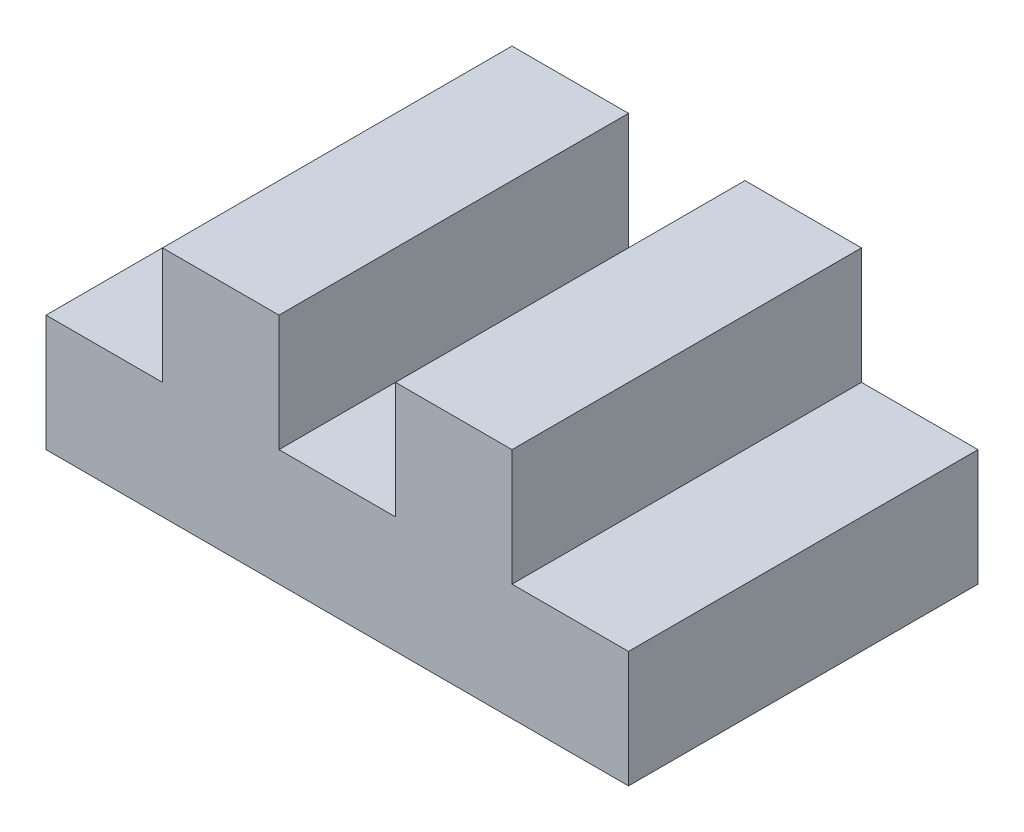
SolidWorks part; units mm, degrees
ref_plane "Front Plane" through (0, 0, 0) normal (0, 0, 1) x (1, 0, 0)
ref_plane "Top Plane" through (0, 0, 0) normal (0, 1, 0) x (1, 0, 0)
ref_plane "Right Plane" through (0, 0, 0) normal (1, 0, 0) x (0, 0, -1)
sketch "Sketch2" plane through (0, 0, 0) normal (0, 0, 1) x (1, 0, 0)
  line L0 (0, 0) -> (50, 0)
  line L1 (50, 0) -> (50, 10)
  line L2 (50, 10) -> (40, 10)
  line L3 (40, 10) -> (40, 20)
  line L4 (40, 20) -> (30, 20)
  line L5 (30, 20) -> (30, 10)
  line L6 (30, 10) -> (20, 10)
  line L7 (20, 10) -> (20, 20)
  line L8 (20, 20) -> (10, 20)
  line L9 (10, 20) -> (10, 10)
  line L10 (10, 10) -> (0, 10)
  line L11 (0, 10) -> (0, 0)
  dimension "D1" = 10
extrude "Boss-Extrude1" add sketch "Sketch2" along normal blind 30
